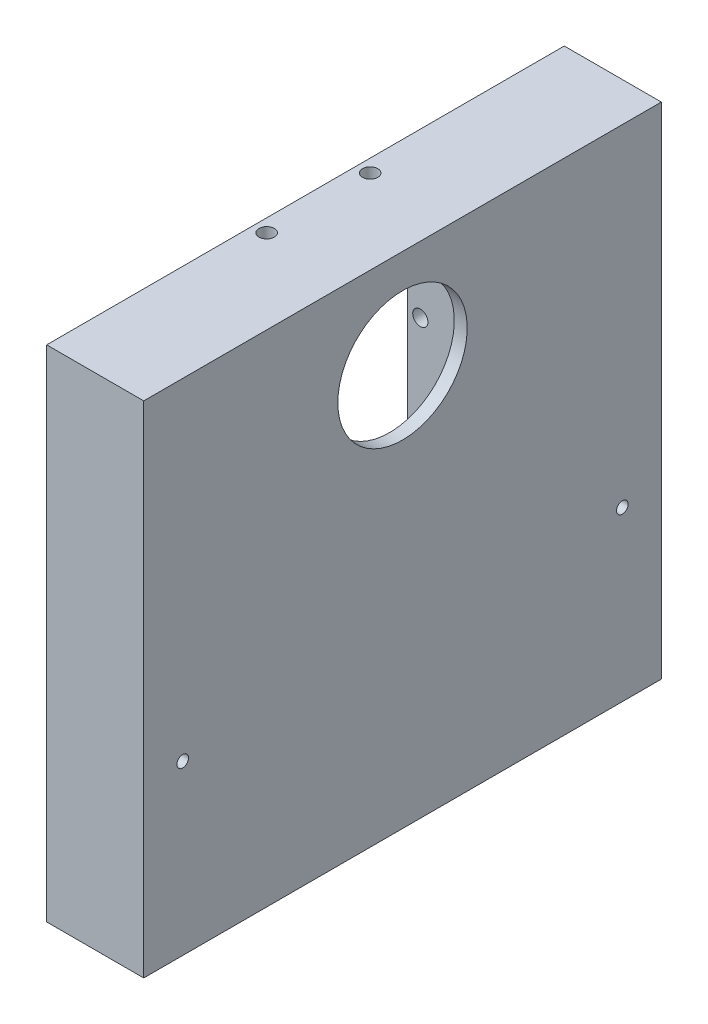
SolidWorks part; units mm, degrees
ref_plane "정면" through (0, 0, 0) normal (0, 0, 1) x (1, 0, 0)
ref_plane "윗면" through (0, 0, 0) normal (0, 1, 0) x (1, 0, 0)
ref_plane "우측면" through (0, 0, 0) normal (1, 0, 0) x (0, 0, -1)
ref_plane "평면1" through (0, 0, 0) normal (-1, 0, 0) x (0, -1, 0)
sketch "스케치1" plane through (0, 0, 0) normal (-1, 0, 0) x (0, -1, 0)
  line L0 (26.75, -54.25) -> (26.75, 25.75)
  line L1 (26.75, 25.75) -> (-73.25, 25.75)
  line L2 (-73.25, 25.75) -> (-73.25, -54.25)
  line L3 (-73.25, -54.25) -> (26.75, -54.25)
extrude "보스-돌출1" add sketch "스케치1" against normal blind 19
sketch "스케치2" plane through (0, 0, 0) normal (-1, 0, 0) x (0, 0, 1)
  line L0 (-50.25, 69.25) -> (-50.25, -22.75)
  line L1 (-50.25, -22.75) -> (21.75, -22.75)
  line L2 (21.75, -22.75) -> (21.75, 69.25)
  line L3 (21.75, 69.25) -> (-50.25, 69.25)
extrude "컷-돌출1" cut sketch "스케치2" against normal blind 17
sketch "스케치3" plane through (17, 0, 0) normal (-1, 0, 0) x (0, 0, 1)
  line L0 (4, 50.5) -> (4, -4)
  line L1 (4, -4) -> (-32.5, -4)
  line L2 (-32.5, -4) -> (-32.5, 50.5)
  line L3 (-32.5, 50.5) -> (4, 50.5)
extrude "보스-돌출2" add sketch "스케치3" along normal blind 17
sketch "스케치4" plane through (0, 0, 0) normal (-1, 0, 0) x (0, 0, 1)
  line L0 (1.5, 48) -> (-30, 48)
  line L1 (-30, 48) -> (-30, -1.5)
  line L2 (-30, -1.5) -> (1.5, -1.5)
  line L3 (1.5, -1.5) -> (1.5, 48)
extrude "컷-돌출2" cut sketch "스케치4" against normal blind 17
hole_wizard "Ø20.0 (20) 지름 구멍1" positions "스케치6" profile "스케치5" hole size "Ø20.0" standard "Ansi Metric"
sketch "스케치6" plane through (17, 0, 0) normal (-1, 0, 0) x (0, 0, 1)
  point P0 (-14.25, 35.25)
sketch "스케치5" plane through (17, 35.25, -14.25) normal (0, 1, 0) x (0, 0, 1)
  line L0 (0, 0) -> (0, 2)
  line L1 (0, 2) -> (10, 2)
  line L2 (10, 2) -> (10, 0)
  line L5 (10, 0) -> (0, 0)
  line L11 (0, -6.35) -> (0, 107.95) construction
  dimension "관통 구멍 지름" = 20
  dimension "관통 구멍 깊이" = 2
hole_wizard "Ø2.35 (2.35) 지름 구멍1" positions "스케치14" profile "스케치13" hole size "Ø2.35" standard "Ansi Metric" end condition up to next
sketch "스케치14" plane through (0, -1.5, 0) normal (0, 1, 0) x (1, 0, 0)
  point P0 (6, 6.25)
  point P1 (6, 22.25)
sketch "스케치13" plane through (6, -1.5, -6.25) normal (1, 0, 0) x (0, 0, 1)
  line L0 (0, 0) -> (0, 2.5)
  line L1 (0, 2.5) -> (1.175, 2.5)
  line L2 (1.175, 2.5) -> (1.175, 0)
  line L5 (1.175, 0) -> (0, 0)
  line L11 (0, -6.35) -> (0, 107.95) construction
  dimension "관통 구멍 지름" = 2.35
  dimension "관통 구멍 깊이" = 2.5
hole_wizard "Ø2.35 (2.35) 지름 구멍2" positions "스케치16" profile "스케치15" hole size "Ø2.35" standard "Ansi Metric" end condition up to next
sketch "스케치16" plane through (0, 0, -30) normal (0, 0, 1) x (1, 0, 0)
  point P0 (6, 27.25)
  point P1 (6, 3.25)
sketch "스케치15" plane through (6, 27.25, -30) normal (1, 0, 0) x (0, -1, 0)
  line L0 (0, 0) -> (0, 2.5)
  line L1 (0, 2.5) -> (1.175, 2.5)
  line L2 (1.175, 2.5) -> (1.175, 0)
  line L5 (1.175, 0) -> (0, 0)
  line L11 (0, -6.35) -> (0, 107.95) construction
  dimension "관통 구멍 지름" = 2.35
  dimension "관통 구멍 깊이" = 2.5
hole_wizard "Ø2.35 (2.35) 지름 구멍3" positions "스케치18" profile "스케치17" hole size "Ø2.35" standard "Ansi Metric" end condition up to next
sketch "스케치18" plane through (0, 48, 0) normal (0, -1, 0) x (-1, 0, 0)
  point P0 (-6, 6.25)
  point P1 (-6, 22.25)
sketch "스케치17" plane through (6, 48, -6.25) normal (1, 0, 0) x (0, 0, -1)
  line L0 (0, 0) -> (0, 2.5)
  line L1 (0, 2.5) -> (1.175, 2.5)
  line L2 (1.175, 2.5) -> (1.175, 0)
  line L5 (1.175, 0) -> (0, 0)
  line L11 (0, -6.35) -> (0, 107.95) construction
  dimension "관통 구멍 지름" = 2.35
  dimension "관통 구멍 깊이" = 2.5
hole_wizard "Ø2.35 (2.35) 지름 구멍4" positions "스케치20" profile "스케치19" hole size "Ø2.35" standard "Ansi Metric" end condition up to next
sketch "스케치20" plane through (0, 0, 1.5) normal (0, 0, -1) x (-1, 0, 0)
  point P0 (-6, 27.25)
  point P1 (-6, 3.25)
sketch "스케치19" plane through (6, 27.25, 1.5) normal (1, 0, 0) x (0, 1, 0)
  line L0 (0, 0) -> (0, 2.5)
  line L1 (0, 2.5) -> (1.175, 2.5)
  line L2 (1.175, 2.5) -> (1.175, 0)
  line L5 (1.175, 0) -> (0, 0)
  line L11 (0, -6.35) -> (0, 107.95) construction
  dimension "관통 구멍 지름" = 2.35
  dimension "관통 구멍 깊이" = 2.5
sketch "스케치21" plane through (0, 73.25, 0) normal (0, 1, 0) x (1, 0, 0)
  line L0 (0, -25.75) -> (0, 54.25) construction
  line L1 (15, -4) -> (0, -4)
  line L2 (15, -4) -> (15, 32.5)
  line L3 (15, 32.5) -> (0, 32.5)
  line L4 (0, -4) -> (0, 32.5)
  line L5 (15, -4) -> (0, 32.5) construction
  line L6 (15, 32.5) -> (0, -4) construction
  line L7 (19, -25.75) -> (19, 54.25) construction
  line L9 (19, 54.25) -> (0, 54.25) construction
  line L10 (19, -25.75) -> (0, -25.75) construction
  point P0 (7.5, 14.25)
  point P7 (15, 14.25)
  dimension "D1" = 0
  dimension "D2" = 4
  dimension "D3" = 36.5
  dimension "D4" = 21.75
  dimension "D5" = 80
sketch "스케치22" plane through (0, -26.75, 0) normal (0, -1, 0) x (1, 0, 0)
  line L0 (0, -54.25) -> (0, 25.75) construction
  line L1 (0, 4) -> (13, 4)
  line L2 (0, 4) -> (0, -32.5)
  line L3 (0, -32.5) -> (13, -32.5)
  line L4 (13, 4) -> (13, -32.5)
  line L5 (0, 4) -> (13, -32.5) construction
  line L6 (0, -32.5) -> (13, 4) construction
  line L7 (19, -54.25) -> (19, 25.75) construction
  line L8 (19, -54.25) -> (0, -54.25) construction
  point P0 (6.5, -14.25)
  dimension "D1" = 36.5
  dimension "D2" = 0
  dimension "D3" = 6
  dimension "D4" = 21.75
extrude "컷-돌출5" cut sketch "스케치22" against normal blind 10
sketch "스케치23" plane through (0, 0, 0) normal (-1, 0, 0) x (0, 0, 1)
  line L0 (-54.25, 73.25) -> (-54.25, -26.75) construction
  line L1 (25.75, 73.25) -> (-54.25, 73.25)
  line L2 (25.75, 73.25) -> (25.75, 50.5)
  line L3 (25.75, 50.5) -> (-54.25, 50.5)
  line L4 (-54.25, 73.25) -> (-54.25, 50.5)
  line L5 (4, 50.5) -> (-32.5, 50.5) construction
  dimension "D1" = 0
extrude "컷-돌출6" cut sketch "스케치23" against normal up to surface (19 mm away) up to face at (19, 35.25, -4.25)
sketch "스케치24" plane through (0, 50.5, 0) normal (0, 1, 0) x (1, 0, 0)
  line L0 (17, 50.25) -> (0, 50.25) construction
  line L1 (17, -21.75) -> (0, -21.75)
  line L2 (17, -21.75) -> (17, -4)
  line L3 (17, -4) -> (0, -4)
  line L4 (0, -21.75) -> (0, -4)
  line L5 (17, 32.5) -> (0, 32.5)
  line L6 (17, 32.5) -> (17, 50.25)
  line L7 (17, 50.25) -> (0, 50.25)
  line L8 (0, 32.5) -> (0, 50.25)
extrude "보스-돌출3" add sketch "스케치24" against normal blind 4
sketch "스케치27" plane through (0, 0, -54.25) normal (0, 0, -1) x (-1, 0, 0)
  line L0 (-19, -26.75) -> (0, -26.75) construction
  line L1 (0, 50.5) -> (-4, 50.5)
  line L2 (0, 50.5) -> (0, -26.75)
  line L3 (0, -26.75) -> (-4, -26.75)
  line L4 (-4, 50.5) -> (-4, -26.75)
  dimension "D1" = 4
extrude "컷-돌출7" cut sketch "스케치27" against normal up to surface (80 mm away) up to face at (9.5, 11.875, 25.75)
sketch "스케치28" plane through (19, 0, 0) normal (1, 0, 0) x (0, 0, -1)
  line L0 (-25.75, -26.75) -> (-25.75, 50.5) construction
  line L1 (54.25, 50.5) -> (54.25, -26.75) construction
  line L3 (54.25, -26.75) -> (-25.75, -26.75) construction
  circle A0 centre (-19.725, -0.75) radius 0.9
  circle A1 centre (48.225, -0.75) radius 0.9
  dimension "D1" = 1.8
  dimension "D2" = 1.8
  dimension "D3" = 6.025
  dimension "D4" = 6.025
  dimension "D5" = 26
  dimension "D6" = 26
extrude "컷-돌출8" cut sketch "스케치28" against normal blind 10
